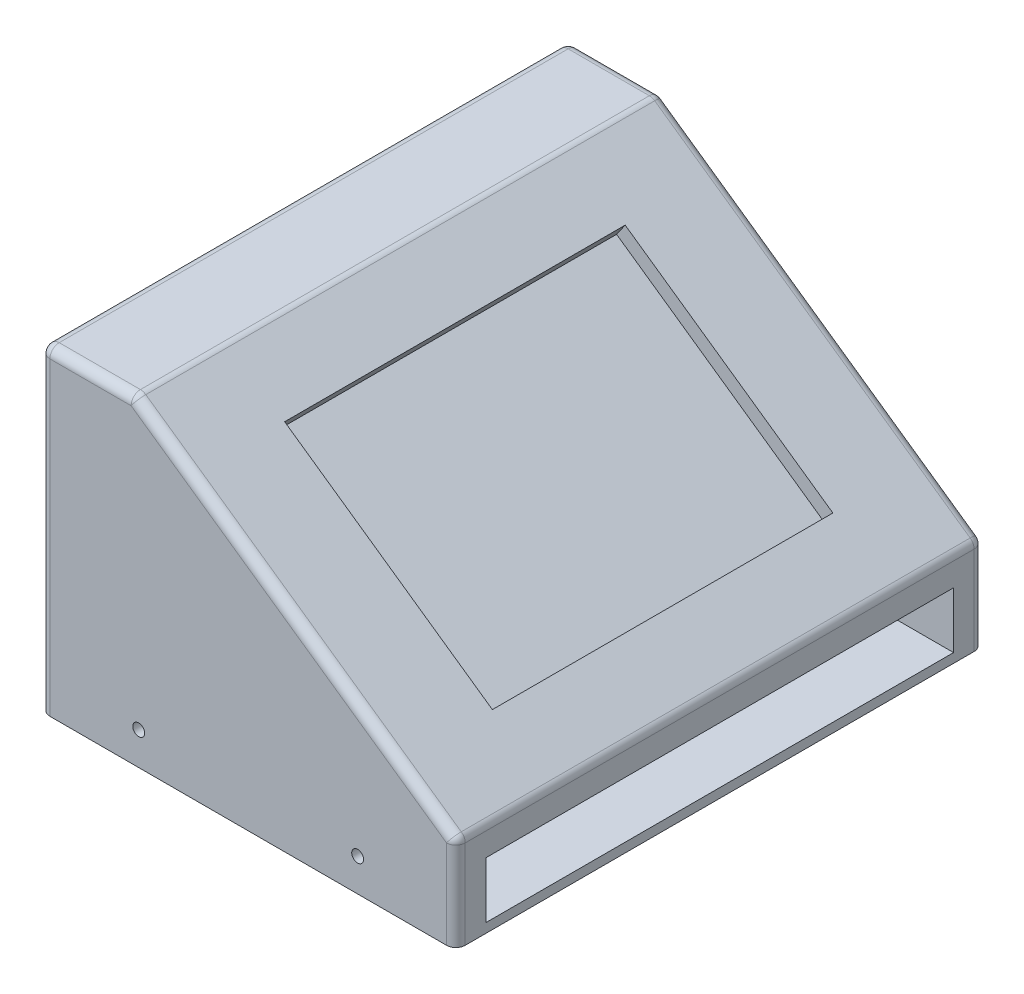
SolidWorks part; units mm, degrees
ref_plane "Front Plane" through (0, 0, 0) normal (0, 0, 1) x (1, 0, 0)
ref_plane "Top Plane" through (0, 0, 0) normal (0, 1, 0) x (1, 0, 0)
ref_plane "Right Plane" through (0, 0, 0) normal (1, 0, 0) x (0, 0, -1)
sketch "Sketch1" plane through (0, 0, 0) normal (0, 0, 1) x (1, 0, 0)
  line L0 (0, 0) -> (0, -50)
  line L1 (0, -50) -> (-222.0219, -50)
  line L2 (0, 0) -> (-172.0219, 120.4511)
  line L3 (-172.0219, 120.4511) -> (-172.0219, -50)
  line L4 (-172.0219, 120.4511) -> (-222.0219, 120.4511)
  line L5 (-222.0219, 120.4511) -> (-222.0219, -50)
  dimension "D1" = 50
  dimension "D2" = 210
  dimension "D3" = 125
  dimension "D4" = 50
extrude "Boss-Extrude1" add sketch "Sketch1" along normal blind 282 contours L4 L5 L1 L3 | L2 L3 L1 L0
sketch "Sketch3" plane through (0, 0, 0) normal (0.5736, 0.8192, 0) x (0.8192, -0.5736, 0)
  line L0 (-210, 0) -> (0, -282)
  line L2 (-172.766, -50) -> (-37.234, -50)
  line L3 (-172.766, -50) -> (-172.766, -232)
  line L4 (-172.766, -232) -> (-37.234, -232)
  line L5 (-37.234, -50) -> (-37.234, -232)
  line L6 (-172.766, -50) -> (-37.234, -232) construction
  line L7 (-172.766, -232) -> (-37.234, -50) construction
  point P4 (-105, -141)
  dimension "D1" = 182
extrude "Cut-Extrude1" cut sketch "Sketch3" against normal blind 8 contours L3 L4 L0 | L5 L2 L0
sketch "Sketch5" plane through (0, 0, 282) normal (0, 0, 1) x (1, 0, 0)
  line L0 (0, 0) -> (0, -50) construction
  line L1 (-222.0219, -50) -> (0, -50)
  line L2 (-222.0219, -50) -> (-222.0219, -45)
  line L3 (-222.0219, -45) -> (0, -45)
  line L4 (0, -50) -> (0, -45)
  line L5 (-222.0219, 120.4511) -> (-222.0219, -50) construction
  line L6 (-182.0219, -45) -> (-157.0219, -45)
  line L7 (-182.0219, -45) -> (-182.0219, -20)
  line L8 (-182.0219, -20) -> (-157.0219, -20)
  line L9 (-157.0219, -45) -> (-157.0219, -20)
  line L10 (-40, -45) -> (-65, -45)
  line L11 (-40, -45) -> (-40, -20)
  line L12 (-40, -20) -> (-65, -20)
  line L13 (-65, -45) -> (-65, -20)
  line L14 (-182.0219, -20) -> (-157.0219, -45)
  line L15 (-40, -20) -> (-65, -45)
  circle A0 centre (-52.5, -32.5) radius 3.175
  circle A1 centre (-169.5219, -32.5) radius 3.175
  dimension "D8" = 6.35
  dimension "D9" = 6.35
  dimension "D1" = 5
  dimension "D2" = 40
  dimension "D3" = 25
  dimension "D4" = 25
  dimension "D5" = 40
  dimension "D6" = 25
  dimension "D7" = 25
extrude "Cut-Extrude3" cut sketch "Sketch5" against normal blind 7.7 contours A0 | A1
sketch "Sketch6" plane through (0, 0, 0) normal (0, 0, -1) x (-1, 0, 0)
  circle A1 centre (169.5219, -32.5) radius 3.175
  circle A2 centre (169.5219, -32.5) radius 3.175
  circle A3 centre (52.5, -32.5) radius 3.175
  circle A4 centre (52.5, -32.5) radius 3.175
  dimension "D2" = 0
  dimension "D3" = 0
extrude "Cut-Extrude4" cut sketch "Sketch6" against normal blind 7.7
fillet "Fillet4" radius 5 11 edges at (0, 0, 141) (-172.0219, 120.4511, 141) (-222.0219, 120.4511, 141) (-222.0219, 35.2255, 0) (-222.0219, 35.2255, 282) (-197.0219, 120.4511, 0) (-197.0219, 120.4511, 282) (-86.011, 60.2255, 0) (-86.011, 60.2255, 282) (0, -25, 0) (0, -25, 282)
sketch "Sketch7" plane through (0, 0, 0) normal (1, 0, 0) x (0, 0, -1)
  line L0 (-277, -50) -> (-5, -50) construction
  line L1 (-266, -50) -> (-16, -50)
  line L2 (-266, -50) -> (-266, -15)
  line L3 (-266, -15) -> (-16, -15)
  line L4 (-16, -50) -> (-16, -15)
  line L6 (-266, -15) -> (-16, -15)
  line L7 (-266, -15) -> (-266, -45)
  line L8 (-266, -45) -> (-16, -45)
  line L9 (-16, -15) -> (-16, -45)
  point P6 (-141, -50)
  point P7 (-141, -50)
  dimension "D1" = 250
  dimension "D2" = 0
  dimension "D3" = 35
  dimension "D4" = 30
extrude "Cut-Extrude6" cut sketch "Sketch7" against normal blind 150 contours L2 L8 L4 L3
sketch "Sketch9" plane through (0, 0, 0) normal (0, 0, -1) x (-1, 0, 0)
  line L0 (64.7247, 39.2168) -> (163.0229, 108.046)
  line L1 (64.7247, 39.2168) -> (70.4604, 31.0253)
  line L2 (163.0229, 108.046) -> (168.7587, 99.8545)
  line L3 (70.4604, 31.0253) -> (168.7587, 99.8545)
  line L4 (173.5984, 115.4511) -> (5, -2.6028) construction
  line L5 (168.7587, 99.8545) -> (70.4604, 31.0253)
  line L6 (168.7587, 99.8545) -> (200.3054, 54.8011)
  line L7 (70.4604, 31.0253) -> (102.0071, -14.0281)
  line L8 (200.3054, 54.8011) -> (102.0071, -14.0281)
  point P6 (89.2992, 56.4241)
  point P7 (113.8738, 73.6314)
  dimension "D1" = 30
  dimension "D2" = 120
  dimension "D3" = 10
  dimension "D4" = 55
extrude "Cut-Extrude7" cut sketch "Sketch9" against normal blind 20 contours L8 L6 L3 L7
fillet "Fillet5" radius 10 4 edges at (-70.4604, 31.0253, 10) (-102.0071, -14.0281, 10) (-168.7587, 99.8545, 10) (-200.3054, 54.8011, 10)
fillet "Fillet6" radius 5 8 edges at (-168.0394, 95.7753, 20) (-184.532, 77.3278, 20) (-196.2262, 55.5204, 20) (-151.1562, 20.3865, 20) (-102.7264, -9.9489, 20) (-86.2338, 8.4986, 20) (-74.5396, 30.306, 20) (-119.6095, 65.4399, 20)
